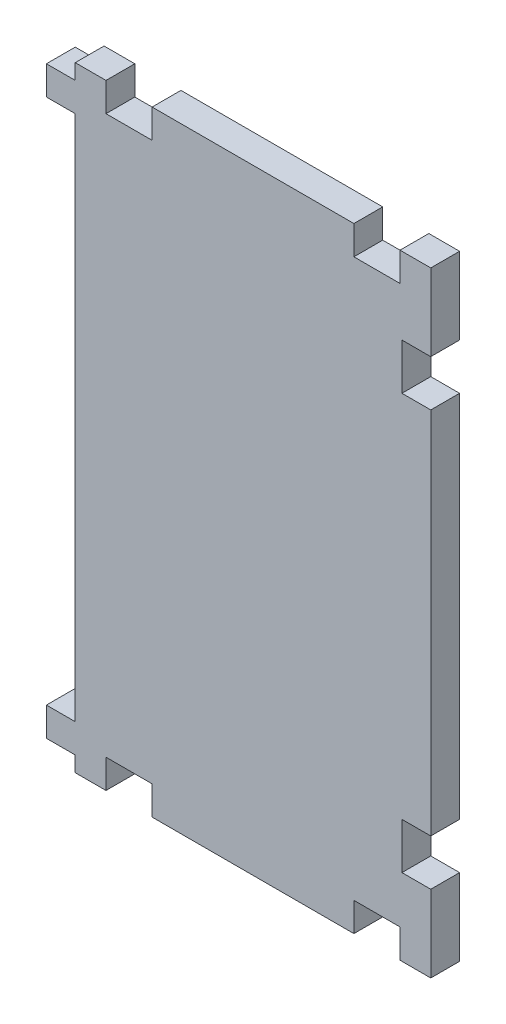
SolidWorks part; units mm, degrees
ref_plane "Front Plane" through (0, 0, 0) normal (0, 0, 1) x (1, 0, 0)
ref_plane "Top Plane" through (0, 0, 0) normal (0, 1, 0) x (1, 0, 0)
ref_plane "Right Plane" through (0, 0, 0) normal (1, 0, 0) x (0, 0, -1)
sketch "Sketch2" plane through (0, 0, 0) normal (0, 0, 1) x (1, 0, 0)
  line L1 (0, 0) -> (0, -101.6)
  line L2 (-4.7625, 0) -> (58.7375, 0)
  line L3 (-4.7625, 0) -> (-4.7625, -101.6)
  line L4 (-4.7625, -101.6) -> (58.7375, -101.6)
  line L5 (58.7375, 0) -> (58.7375, -101.6)
  line L6 (-4.7625, -2.54) -> (0, -2.54)
  line L7 (-4.7625, -2.54) -> (-4.7625, -7.3025)
  line L8 (-4.7625, -7.3025) -> (0, -7.3025)
  line L9 (0, -2.54) -> (0, -7.3025)
  line L10 (-4.7625, -94.2975) -> (0, -94.2975)
  line L11 (-4.7625, -94.2975) -> (-4.7625, -99.06)
  line L12 (-4.7625, -99.06) -> (0, -99.06)
  line L13 (0, -94.2975) -> (0, -99.06)
  line L15 (5.08, 0) -> (12.7, 0)
  line L16 (5.08, 0) -> (5.08, -4.7625)
  line L17 (5.08, -4.7625) -> (12.7, -4.7625)
  line L18 (12.7, 0) -> (12.7, -4.7625)
  line L19 (46.0375, 0) -> (53.6575, 0)
  line L20 (46.0375, 0) -> (46.0375, -4.7625)
  line L21 (46.0375, -4.7625) -> (53.6575, -4.7625)
  line L22 (53.6575, 0) -> (53.6575, -4.7625)
  line L23 (5.08, -101.6) -> (12.7, -101.6)
  line L24 (5.08, -101.6) -> (5.08, -96.8375)
  line L25 (5.08, -96.8375) -> (12.7, -96.8375)
  line L26 (12.7, -101.6) -> (12.7, -96.8375)
  line L27 (46.0375, -101.6) -> (53.6575, -101.6)
  line L28 (46.0375, -101.6) -> (46.0375, -96.8375)
  line L29 (46.0375, -96.8375) -> (53.6575, -96.8375)
  line L30 (53.6575, -101.6) -> (53.6575, -96.8375)
  line L31 (58.7375, -88.9) -> (53.975, -88.9)
  line L32 (58.7375, -88.9) -> (58.7375, -81.28)
  line L33 (58.7375, -81.28) -> (53.975, -81.28)
  line L34 (53.975, -88.9) -> (53.975, -81.28)
  line L35 (58.7375, -20.32) -> (53.975, -20.32)
  line L36 (58.7375, -20.32) -> (58.7375, -12.7)
  line L37 (58.7375, -12.7) -> (53.975, -12.7)
  line L38 (53.975, -20.32) -> (53.975, -12.7)
  line M30 (0, -7.3025) -> (0, -2.54)
  line M31 (0, -2.54) -> (-4.7625, -2.54)
  line M32 (-4.7625, -2.54) -> (-4.7625, -7.3025)
  line M33 (-4.7625, -7.3025) -> (0, -7.3025)
  dimension "D1" = 63.5
  dimension "D2" = 7.62
  dimension "D3" = 4.7625
  dimension "D4" = 5.08
  dimension "D5" = 5.08
  dimension "D6" = 5.08
  dimension "D7" = 5.08
  dimension "D8" = 4.7625
  dimension "D9" = 7.62
  dimension "D10" = 12.7
  dimension "D11" = 12.7
extrude "Boss-Extrude1" add sketch "Sketch2" along normal blind 4.7625 contours L3 L12 L1 L10 | M33 M30 M31 M32 | L35 L38 L37 L5 L2 L22 L21 L20 L18 L17 L16 L1 L4 L24 L25 L26 L28 L29 L30 L31 L34 L33 M30
